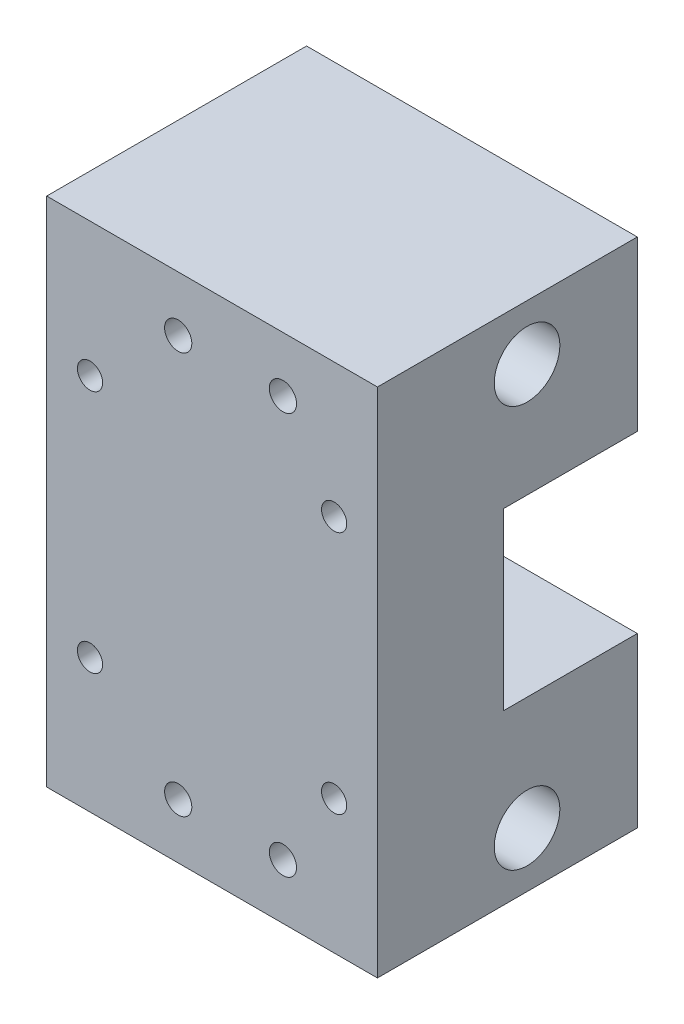
SolidWorks part; units mm, degrees
ref_plane "Plano frontal" through (0, 0, 0) normal (0, 0, 1) x (1, 0, 0)
ref_plane "Plano superior" through (0, 0, 0) normal (0, 1, 0) x (1, 0, 0)
ref_plane "Plano direito" through (0, 0, 0) normal (1, 0, 0) x (0, 0, -1)
ref_plane "Plano1" through (0, 0, 21) normal (0, 0, 1) x (1, 0, 0)
sketch "Esboço1" plane through (0, 0, 21) normal (0, 0, 1) x (1, 0, 0)
  line L0 (0, 65) -> (0, 0)
  line L1 (0, 0) -> (42, 0)
  line L2 (42, 0) -> (42, 65)
  line L3 (42, 65) -> (0, 65)
extrude "Ressalto-extrusão1" add sketch "Esboço1" against normal blind 21
sketch "Esboço2" plane through (42, 0, 0) normal (1, 0, 0) x (0, 0, -1)
  line L0 (0, 21.3875) -> (0, 43.6125)
  line L1 (0, 43.6125) -> (-17, 43.6125)
  line L2 (-17, 43.6125) -> (-17, 21.3875)
  line L3 (-17, 21.3875) -> (0, 21.3875)
extrude "Corte-extrusão1" cut sketch "Esboço2" against normal through all
hole_wizard "Furo com folga de M31" positions "Esboço4" profile "Esboço3" hole size "M3" standard "Ansi Metric"
sketch "Esboço4" plane through (0, 0, 0) normal (0, 0, -1) x (-1, 0, 0)
  point P0 (-30, 7)
  point P1 (-16.7, 7)
  point P2 (-16.7, 58)
  point P3 (-30, 58)
sketch "Esboço3" plane through (30, 7, 0) normal (1, 0, 0) x (0, 1, 0)
  line L0 (0, 0) -> (0, 21)
  line L1 (0, 21) -> (1.7272, 21)
  line L2 (1.7272, 21) -> (1.7272, 0)
  line L5 (1.7272, 0) -> (0, 0)
  line L11 (0, -6.35) -> (0, 107.95) construction
  dimension "Thru Hole Dia." = 3.4544
  dimension "Thru Hole Depth" = 21
hole_wizard "Furo com folga de M201" positions "Esboço6" profile "Esboço5" hole size "M20" standard "Ansi Metric"
sketch "Esboço6" plane through (0, 0, 21) normal (0, 0, 1) x (1, 0, 0)
  point P0 (21, 32.5)
sketch "Esboço5" plane through (21, 32.5, 21) normal (1, 0, 0) x (0, -1, 0)
  line L0 (0, 0) -> (0, 21)
  line L1 (0, 21) -> (11.1125, 21)
  line L2 (11.1125, 21) -> (11.1125, 0)
  line L5 (11.1125, 0) -> (0, 0)
  line L11 (0, -6.35) -> (0, 107.95) construction
  dimension "Thru Hole Dia." = 22.225
  dimension "Thru Hole Depth" = 21
hole_wizard "Rebaixo para parafuso de máquina de cabeça sextavada de M31" positions "Esboço8" profile "Esboço7" counterbore size "M3" standard "Ansi Metric"
sketch "Esboço8" plane through (0, 0, 0) normal (0, 0, -1) x (-1, 0, 0)
  point P0 (-36.5, 17)
  point P1 (-5.5, 17)
  point P2 (-5.5, 48)
  point P3 (-36.5, 48)
sketch "Esboço7" plane through (36.5, 17, 0) normal (1, 0, 0) x (0, 1, 0)
  line L0 (0, 0) -> (0, 21)
  line L1 (0, 21) -> (1.6, 21)
  line L3 (1.6, 21) -> (1.6, 7.62)
  line L4 (1.6, 7.62) -> (3, 7.62)
  line L5 (3, 7.62) -> (3, 0)
  line L7 (3, 0) -> (0, 0)
  line L11 (0, -6.35) -> (0, 107.95) construction
  dimension "Thru Hole Dia." = 3.2
  dimension "Thru Hole Depth" = 21
  dimension "C'Bore Dia." = 6
  dimension "C'Bore Depth" = 7.62
hole_wizard "Furo1" positions "Esboço10" profile "Esboço9" legacy
sketch "Esboço10" plane through (42, 0, 0) normal (1, 0, 0) x (0, 0, -1)
  point P0 (-14, 7)
  point P1 (-14, 58)
sketch "Esboço9" plane through (42, 7, 14) normal (0, 1, 0) x (0, 0, -1)
  line L0 (0, 0) -> (0, 8)
  line L1 (0, 8) -> (4.1672, 8)
  line L2 (4.1672, 8) -> (4.1672, 0)
  line L3 (4.1672, 0) -> (0, 0)
  line L4 (0, 110) -> (0, -10) construction
  dimension "Diameter" = 8.3344
  dimension "Depth" = 8
sketch "Esboço11" plane through (0, 0, 21) normal (0, 0, 1) x (1, 0, 0)
  circle A0 centre (21, 32.5) radius 5.5
  circle A1 centre (21, 32.5) radius 11.1125
  dimension "D1" = 11
extrude "Ressalto-extrusão2" add sketch "Esboço11" against normal blind 4
sketch "Esboço12" plane through (0, 0, 21) normal (0, 0, 1) x (1, 0, 0)
  line L1 (0, 0) -> (42, 0)
  line L2 (0, 0) -> (0, 65)
  line L3 (0, 65) -> (42, 65)
  line L4 (42, 0) -> (42, 65)
  circle A0 centre (21, 32.5) radius 5.5
  circle A1 centre (5.5, 48) radius 1.6
  circle A2 centre (16.7, 58) radius 1.7272
  circle A3 centre (30, 58) radius 1.7272
  circle A4 centre (36.5, 48) radius 1.6
  circle A5 centre (36.5, 17) radius 1.6
  circle A6 centre (5.5, 17) radius 1.6
  circle A7 centre (16.7, 7) radius 1.7272
  circle A8 centre (30, 7) radius 1.7282
extrude "Ressalto-extrusão3" add sketch "Esboço12" along normal blind 12
sketch "Esboço14" plane through (0, 0, 33) normal (0, 0, 1) x (1, 0, 0)
  circle A0 centre (21, 32.5) radius 5.5
extrude "Ressalto-extrusão4" add sketch "Esboço14" against normal blind 4
